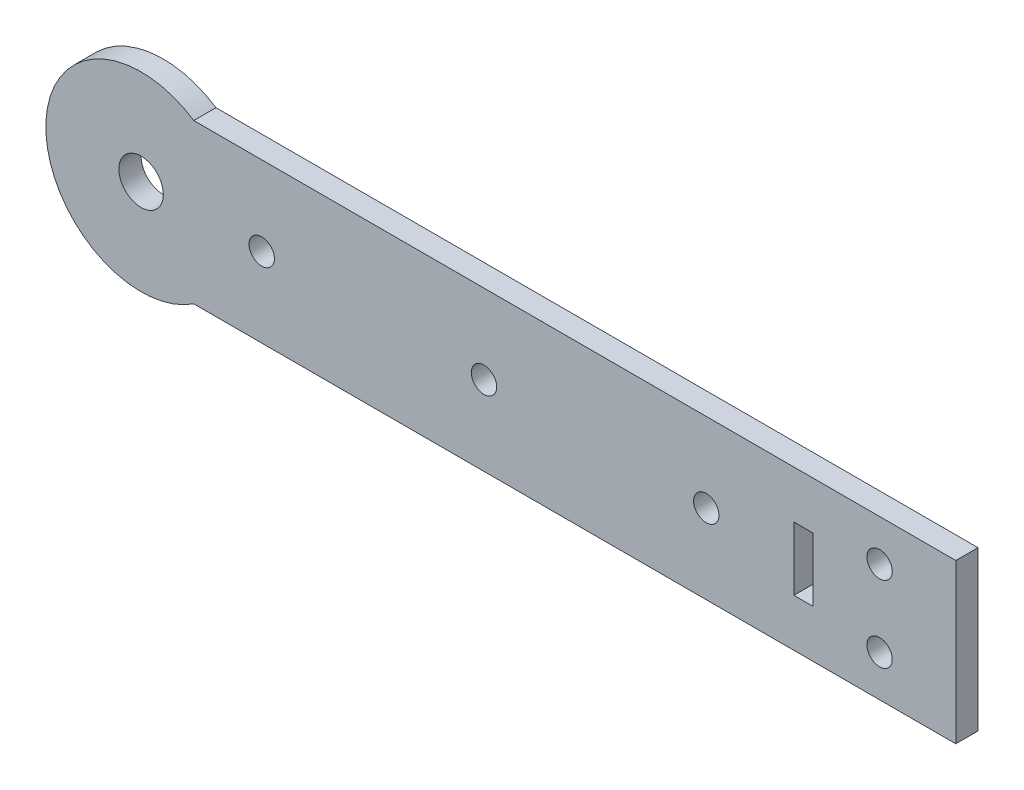
SolidWorks part; units mm, degrees
material "Balsa"
ref_plane "Alzado" through (0, 0, 0) normal (0, 0, 1) x (1, 0, 0)
ref_plane "Planta" through (0, 0, 0) normal (0, 1, 0) x (1, 0, 0)
ref_plane "Vista lateral" through (0, 0, 0) normal (1, 0, 0) x (0, 0, -1)
sketch "Croquis1" plane through (0, 0, 0) normal (0, 0, 1) x (1, 0, 0)
  line L0 (36.8051, 12.5) -> (36.8051, -12.5)
  line L5 (-83.1949, 12.5) -> (36.8051, 12.5)
  line L7 (-83.1949, -12.5) -> (36.8051, -12.5)
  line L8 (0, 0) -> (-8.8431, 0) construction
  line L10 (11.3051, 5) -> (14.3051, 5)
  line L11 (11.3051, 5) -> (11.3051, -5)
  line L12 (11.3051, -5) -> (14.3051, -5)
  line L13 (14.3051, 5) -> (14.3051, -5)
  line L14 (11.3051, 5) -> (14.3051, -5) construction
  line L15 (11.3051, -5) -> (14.3051, 5) construction
  arc A13 (-83.1949, 12.5) -> (-83.1949, -12.5) centre (-91.4865, 0) ccw
  circle A15 centre (-91.4865, 0) radius 3.5
  circle A16 centre (-72.4865, 0) radius 2
  circle A17 centre (24.8051, 6) radius 2
  circle A18 centre (24.8051, -6) radius 2
  circle A19 centre (-37.4865, 0) radius 2
  circle A20 centre (-2.4865, 0) radius 2
  point P0 (0, 0)
  point P20 (12.8051, 0)
  point P25 (0, 0)
  dimension "D2" = 25
  dimension "D3" = 30
  dimension "D4" = 7
  dimension "D5" = 19
  dimension "D9" = 12
  dimension "D10" = 4
  dimension "D8" = 4
  dimension "D1" = 120
  dimension "D6" = 12.5
  dimension "D7" = 12
  dimension "D11" = 35
  dimension "D12" = 35
  dimension "D13" = 3
  dimension "D14" = 10
  dimension "D15" = 12.5
  dimension "D16" = 24
  dimension "D17" = 12.5
extrude "Saliente-Extruir2" add sketch "Croquis1" along normal blind 3.5
